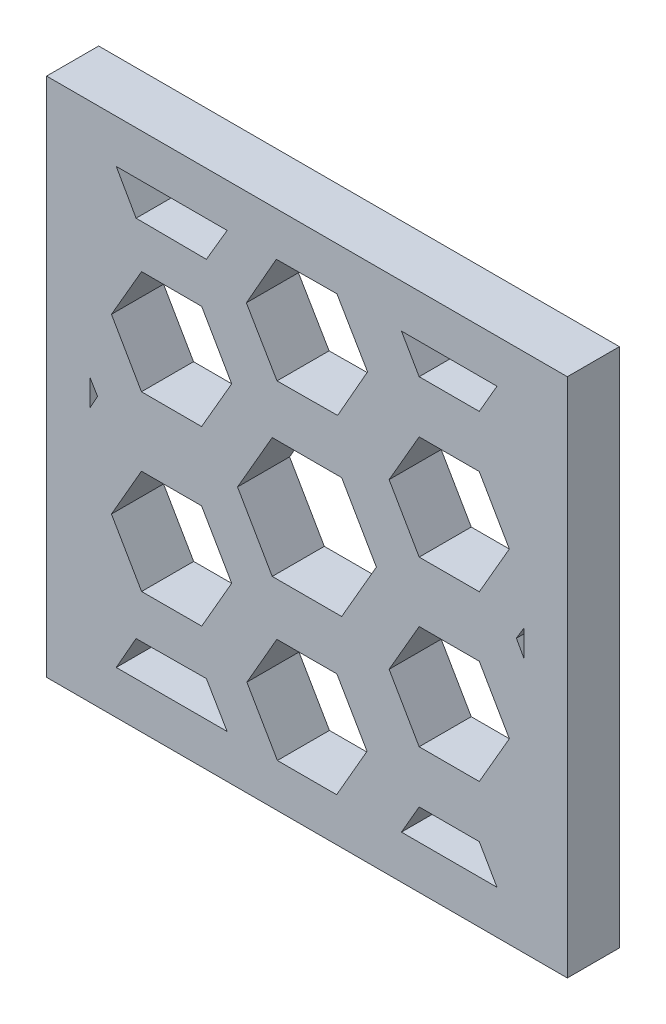
SolidWorks part; units mm, degrees
ref_plane "Alzado" through (0, 0, 0) normal (0, 0, 1) x (1, 0, 0)
ref_plane "Planta" through (0, 0, 0) normal (0, 1, 0) x (1, 0, 0)
ref_plane "Vista lateral" through (0, 0, 0) normal (1, 0, 0) x (0, 0, -1)
sketch "Croquis1" plane through (0, 0, 0) normal (0, 0, 1) x (1, 0, 0)
  line L0 (11, -5.7978) -> (11, -5.875)
  line L1 (-15, 15) -> (15, 15)
  line L2 (-15, 15) -> (-15, -15)
  line L3 (-15, -15) -> (15, -15)
  line L4 (15, 15) -> (15, -15)
  line L5 (-2.5359, -2.5359) -> (15, 15) construction
  line L6 (-7.9784, -7.9784) -> (-7.9732, -7.9732) construction
  line L7 (-2.5739, -11) -> (-2.5736, -11)
  line L8 (-11, -5.4369) -> (-11, -4.5272)
  line L10 (11, -5.875) -> (11, -5.7978)
  line L11 (-7.9784, -7.9784) -> (-7.9732, -7.9732) construction
  line L12 (-2.5359, -2.5359) -> (12.5, 12.5) construction
  line L13 (4, 0) -> (2, 3.4641)
  line L14 (2, 3.4641) -> (-2, 3.4641)
  line L15 (-2, 3.4641) -> (-4, 0)
  line L16 (-4, 0) -> (-2, -3.4641)
  line L17 (-2, -3.4641) -> (2, -3.4641)
  line L18 (2, -3.4641) -> (4, 0)
  line L19 (5.5981, -3.2321) -> (5.5985, -3.2323)
  line L20 (5.5981, -3.2321) -> (5.5985, -3.2323)
  line L22 (10.6354, -2.9576) -> (11.6597, -4.7329)
  line L23 (6.4651, -1.7321) -> (4.7326, -4.7312)
  line L24 (4.7326, -4.7312) -> (6.4636, -7.7312)
  line L25 (6.4636, -7.7312) -> (9.9272, -7.7321)
  line L26 (9.9272, -7.7321) -> (11, -5.875)
  line L27 (11, -3.5895) -> (9.9287, -1.7329)
  line L28 (9.9287, -1.7329) -> (6.4651, -1.7321)
  line L29 (10.4636, -6.8035) -> (11.6597, -4.7329)
  line L30 (4.7326, -4.7312) -> (4.7317, -4.7317)
  line L34 (1.7252, -6.4641) -> (-1.7355, -6.47)
  line L35 (-1.7355, -6.47) -> (-3.4607, -9.47)
  line L36 (-3.4607, -9.47) -> (-1.7252, -12.4641)
  line L37 (1.7355, -12.4582) -> (1.7489, -12.4581)
  line L38 (1.7355, -12.4582) -> (3.4607, -9.4582)
  line L39 (3.4607, -9.4582) -> (1.7252, -6.4641)
  line L45 (-3.4641, 0) -> (-4, 0)
  line L46 (-4.3361, -4.9745) -> (-6.0716, -1.9775)
  line L47 (-6.0716, -1.9775) -> (-9.5348, -1.9819)
  line L48 (-9.5348, -1.9819) -> (-11.2626, -4.9834)
  line L49 (-11.2626, -4.9834) -> (-9.5271, -7.9804)
  line L50 (-9.5271, -7.9804) -> (-6.0639, -7.976)
  line L51 (-6.0639, -7.976) -> (-4.3361, -4.9745)
  line L52 (9.9287, 1.7329) -> (6.4651, 1.7321)
  line L53 (11, 3.5895) -> (9.9287, 1.7329)
  line L54 (9.9272, 7.7321) -> (11, 5.875)
  line L55 (6.4636, 7.7312) -> (9.9272, 7.7321)
  line L56 (4.7326, 4.7312) -> (6.4636, 7.7312)
  line L57 (6.4651, 1.7321) -> (4.7326, 4.7312)
  line L58 (3.4607, 9.4582) -> (1.7252, 6.4641)
  line L59 (2.574, 11) -> (3.4607, 9.4582)
  line L61 (-3.4607, 9.47) -> (-2.5739, 11)
  line L62 (-1.7355, 6.47) -> (-3.4607, 9.47)
  line L63 (1.7252, 6.4641) -> (-1.7355, 6.47)
  line L64 (-6.0639, 7.976) -> (-4.3361, 4.9745)
  line L65 (-9.5271, 7.9804) -> (-6.0639, 7.976)
  line L66 (-11, 5.4369) -> (-9.5271, 7.9804)
  line L67 (-9.5348, 1.9819) -> (-11, 4.5272)
  line L68 (-6.0716, 1.9775) -> (-9.5348, 1.9819)
  line L69 (-4.3361, 4.9745) -> (-6.0716, 1.9775)
  line L70 (2.574, 11) -> (2.605, 11)
  line L73 (-1.7252, -12.4641) -> (-1.7044, -12.5)
  line L75 (1.7882, -12.3665) -> (1.7114, -12.5)
  line L76 (-10.9878, -12.5) -> (-4.5982, -12.5)
  line L77 (-12.5, -0.2976) -> (-12.5, 1.211)
  line L78 (-10.9878, 12.5) -> (-4.5982, 12.5)
  line L79 (12.5, -0.2976) -> (12.5, 1.211)
  line L80 (-7.9784, -7.9784) -> (-7.9732, -7.9732) construction
  line L81 (-2.5359, -2.5359) -> (11, 11) construction
  line L82 (5.4429, -12.5) -> (10.9479, -12.5)
  line L83 (-3.4607, 9.47) -> (3.4607, 9.4582)
  line L84 (5.4429, 12.5) -> (10.9479, 12.5)
  line L85 (1.7252, 12.5) -> (-1.7666, 12.4761)
  line L86 (-1.7666, 12.4761) -> (-3.4918, 9.4402)
  line L87 (-3.4918, 9.4402) -> (-1.7252, 6.4282)
  line L88 (-1.7252, 6.4282) -> (1.7666, 6.4521)
  line L89 (1.7666, 6.4521) -> (3.4918, 9.488)
  line L90 (3.4918, 9.488) -> (1.7252, 12.5)
  line L91 (11, 5.875) -> (11.6597, 4.7329)
  line L92 (11, 3.5895) -> (11.6597, 4.7329)
  line L93 (-1.7044, -12.5) -> (1.7114, -12.5)
  line L94 (-5.7959, 10.4584) -> (-4.5982, 12.5)
  line L98 (-10.9878, 12.5) -> (-9.8439, 10.4866)
  line L99 (-9.8439, 10.4866) -> (-5.7959, 10.4584)
  line L100 (-2.5359, 2.5359) -> (7.7315, -7.7315) construction
  line L101 (-2.5359, 2.5359) -> (7.7315, -7.7315) construction
  line L102 (-2.5359, 2.5359) -> (7.7315, -7.7315) construction
  line L103 (9.9272, 10.7321) -> (10.9479, 12.5)
  line L107 (5.4429, 12.5) -> (6.4636, 10.7321)
  line L108 (6.4636, 10.7321) -> (9.9272, 10.7321)
  line L109 (6.4636, -10.7321) -> (9.9272, -10.7321)
  line L110 (5.4429, -12.5) -> (6.4636, -10.7321)
  line L114 (9.9272, -10.7321) -> (10.9479, -12.5)
  line L115 (-9.8439, -10.4866) -> (-5.7959, -10.4584)
  line L116 (-10.9878, -12.5) -> (-9.8439, -10.4866)
  line L120 (-5.7959, -10.4584) -> (-4.5982, -12.5)
  line L121 (-10.4017, 6.47) -> (-11.2626, 4.9834)
  line L122 (-10.2674, 3.2545) -> (-10.4603, 3.5895)
  line L123 (-10.63, 3.8844) -> (-11.2626, 4.9834)
  line L124 (-2.6054, 11) -> (-2.5739, 11)
  line L125 (2.5736, -11) -> (2.574, -11)
  line L134 (-12.5, -0.2976) -> (-12.0649, 0.4844)
  line L135 (-12.0649, 0.4844) -> (-12.5, 1.211)
  line L136 (12.0649, 0.4844) -> (12.5, 1.211)
  line L137 (12.5, -0.2976) -> (12.0649, 0.4844)
  line L142 (-18.2122, 1.902) -> (-19.0628, 0.373) [skipped]
  line L143 (-19.0628, 0.373) -> (-18.1639, -1.1281) [skipped]
  line L144 (-15.5156, -2.6014) -> (-15, -2.5932) [skipped]
  line L146 (-15, 3.4686) -> (-15.6121, 3.4589) [skipped]
  line L147 (-5.7471, 17.4698) -> (-9.7951, 17.498) [skipped]
  line L148 (-10.8193, 15.7522) -> (-11.2606, 15) [skipped]
  line L149 (-4.344, 15) -> (-4.7473, 15.7099) [skipped]
  line L150 (9.9272, 16.7312) -> (6.4636, 16.7312) [skipped]
  line L151 (10.9267, 15) -> (10.7931, 15.2314) [skipped]
  line L152 (5.5973, 15.2307) -> (5.4637, 14.9993) [skipped]
  circle A0 centre (0, 0) radius 3.4641 construction
  arc A1 (10.7942, -3.2329) -> (11, -5.7978) centre (8.1962, -4.7321) ccw construction
  circle A2 centre (0, -9.4641) radius 2.997 construction
  circle A3 centre (-7.7994, -4.9789) radius 2.9993 construction
  circle A4 centre (0, 9.4641) radius 3.024 construction
  arc A5 (10.7931, 12.2318) -> (10.9304, 12.5) centre (8.1954, 13.7316) ccw construction
  arc A6 (5.4603, 12.5) -> (5.5977, 12.2318) centre (8.1954, 13.7316) ccw construction
  arc A7 (-4.7717, 12.2042) -> (-4.6166, 12.5) centre (-7.7955, 13.9782) ccw construction
  point P0 (0, 0)
  point P6 (0, 0)
  point P81 (-15, 0)
  dimension "D1" = 30
  dimension "D2" = 30
  dimension "D4" = 4
  dimension "D5" = 4
  dimension "D6" = 2.5
  dimension "D7" = 3
  dimension "D11" = 2.5
  dimension "D16" = 3
  dimension "D20" = 3
extrude "Saliente-Extruir3" add sketch "Croquis1" along normal blind 3
